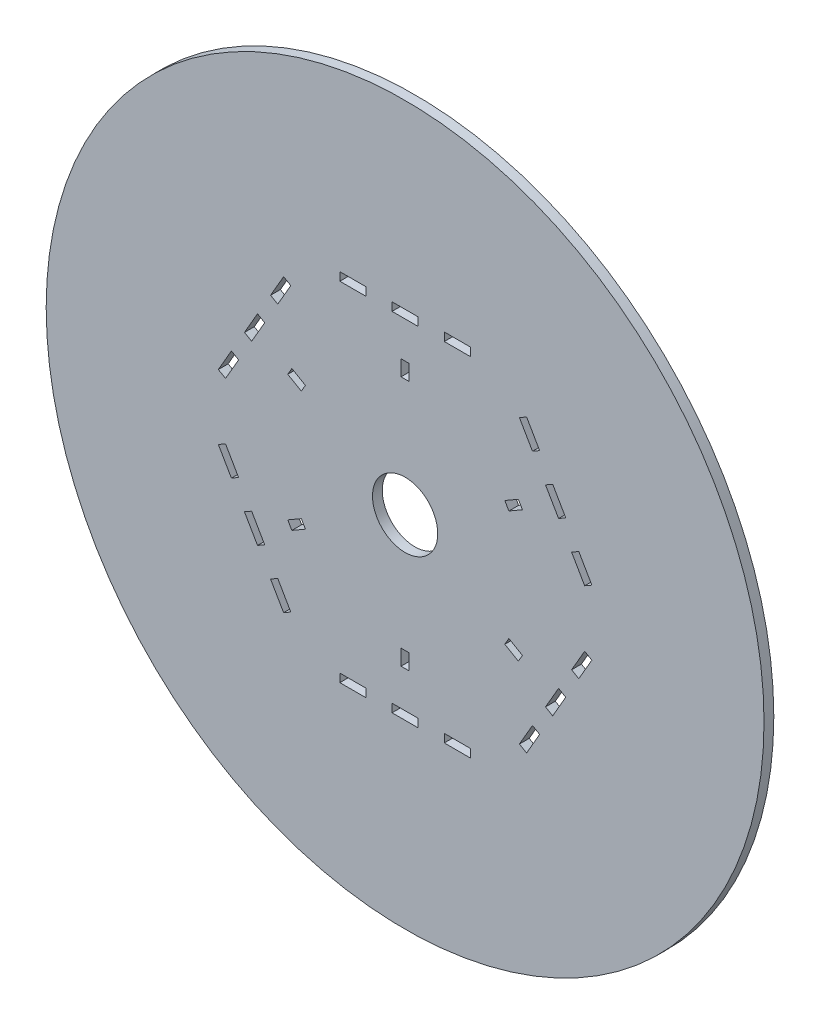
SolidWorks part; units mm, degrees
ref_plane "Front Plane" through (0, 0, 0) normal (0, 0, 1) x (1, 0, 0)
ref_plane "Top Plane" through (0, 0, 0) normal (0, 1, 0) x (1, 0, 0)
ref_plane "Right Plane" through (0, 0, 0) normal (1, 0, 0) x (0, 0, -1)
sketch "Sketch1" plane through (0, 0, 0) normal (0, 0, 1) x (1, 0, 0)
  line L0 (5, 68.175) -> (-5, 68.175)
  line L1 (-5, 68.175) -> (-5, 65)
  line L2 (-5, 65) -> (5, 65)
  line L3 (-15, 68.175) -> (-5, 68.175) construction
  line L4 (-15, 68.175) -> (-25, 68.175)
  line L5 (-15, 68.175) -> (-15, 65)
  line L6 (-15, 65) -> (-25, 65)
  line L7 (-25, 68.175) -> (-25, 65)
  line L8 (25, 68.175) -> (25, 65)
  line L9 (15, 65) -> (25, 65)
  line L10 (15, 68.175) -> (15, 65)
  line L11 (15, 68.175) -> (25, 68.175)
  line L12 (15, 68.175) -> (5, 68.175) construction
  line L13 (5, 68.175) -> (5, 65)
  line L14 (1.5625, 51) -> (-1.5625, 51)
  line L15 (-1.5625, 51) -> (-1.5625, 45)
  line L16 (-1.5625, 45) -> (1.5625, 45)
  line L17 (1.5625, 51) -> (1.5625, 45)
  line L18 (0, 65) -> (0, 51) construction
  line L19 (0, 45) -> (0, 0) construction
  line L20 (61.5413, 29.7574) -> (56.5413, 38.4176)
  line L21 (56.5413, 38.4176) -> (53.7917, 36.8301)
  line L22 (53.7917, 36.8301) -> (58.7917, 28.1699)
  line L23 (51.5413, 47.0779) -> (46.5413, 55.7381)
  line L24 (51.5413, 47.0779) -> (48.7917, 45.4904)
  line L25 (48.7917, 45.4904) -> (43.7917, 54.1506)
  line L26 (46.5413, 55.7381) -> (43.7917, 54.1506)
  line L27 (71.5413, 12.4369) -> (68.7917, 10.8494)
  line L28 (63.7917, 19.5096) -> (68.7917, 10.8494)
  line L29 (66.5413, 21.0971) -> (63.7917, 19.5096)
  line L30 (66.5413, 21.0971) -> (71.5413, 12.4369)
  line L31 (61.5413, 29.7574) -> (58.7917, 28.1699)
  line L32 (44.9485, 24.1468) -> (43.386, 26.8532)
  line L33 (43.386, 26.8532) -> (38.1899, 23.8532)
  line L34 (38.1899, 23.8532) -> (39.7524, 21.1468)
  line L35 (44.9485, 24.1468) -> (39.7524, 21.1468)
  line L36 (51.5413, 47.0779) -> (56.5413, 38.4176) construction
  line L37 (66.5413, 21.0971) -> (61.5413, 29.7574) construction
  line L38 (56.2917, 32.5) -> (44.1673, 25.5) construction
  line L39 (56.5413, -38.4176) -> (61.5413, -29.7574)
  line L40 (61.5413, -29.7574) -> (58.7917, -28.1699)
  line L41 (58.7917, -28.1699) -> (53.7917, -36.8301)
  line L42 (66.5413, -21.0971) -> (71.5413, -12.4369)
  line L43 (66.5413, -21.0971) -> (63.7917, -19.5096)
  line L44 (63.7917, -19.5096) -> (68.7917, -10.8494)
  line L45 (71.5413, -12.4369) -> (68.7917, -10.8494)
  line L46 (46.5413, -55.7381) -> (43.7917, -54.1506)
  line L47 (48.7917, -45.4904) -> (43.7917, -54.1506)
  line L48 (51.5413, -47.0779) -> (48.7917, -45.4904)
  line L49 (51.5413, -47.0779) -> (46.5413, -55.7381)
  line L50 (56.5413, -38.4176) -> (53.7917, -36.8301)
  line L51 (43.386, -26.8532) -> (44.9485, -24.1468)
  line L52 (44.9485, -24.1468) -> (39.7524, -21.1468)
  line L53 (39.7524, -21.1468) -> (38.1899, -23.8532)
  line L54 (43.386, -26.8532) -> (38.1899, -23.8532)
  line L55 (66.5413, -21.0971) -> (61.5413, -29.7574) construction
  line L56 (51.5413, -47.0779) -> (56.5413, -38.4176) construction
  line L57 (56.2917, -32.5) -> (44.1673, -25.5) construction
  line L58 (-5, -68.175) -> (5, -68.175)
  line L59 (5, -68.175) -> (5, -65)
  line L60 (5, -65) -> (-5, -65)
  line L61 (15, -68.175) -> (25, -68.175)
  line L62 (15, -68.175) -> (15, -65)
  line L63 (15, -65) -> (25, -65)
  line L64 (25, -68.175) -> (25, -65)
  line L65 (-25, -68.175) -> (-25, -65)
  line L66 (-15, -65) -> (-25, -65)
  line L67 (-15, -68.175) -> (-15, -65)
  line L68 (-15, -68.175) -> (-25, -68.175)
  line L69 (-5, -68.175) -> (-5, -65)
  line L70 (-1.5625, -51) -> (1.5625, -51)
  line L71 (1.5625, -51) -> (1.5625, -45)
  line L72 (1.5625, -45) -> (-1.5625, -45)
  line L73 (-1.5625, -51) -> (-1.5625, -45)
  line L74 (15, -68.175) -> (5, -68.175) construction
  line L75 (-15, -68.175) -> (-5, -68.175) construction
  line L76 (0, -65) -> (0, -51) construction
  line L77 (-61.5413, -29.7574) -> (-56.5413, -38.4176)
  line L78 (-56.5413, -38.4176) -> (-53.7917, -36.8301)
  line L79 (-53.7917, -36.8301) -> (-58.7917, -28.1699)
  line L80 (-51.5413, -47.0779) -> (-46.5413, -55.7381)
  line L81 (-51.5413, -47.0779) -> (-48.7917, -45.4904)
  line L82 (-48.7917, -45.4904) -> (-43.7917, -54.1506)
  line L83 (-46.5413, -55.7381) -> (-43.7917, -54.1506)
  line L84 (-71.5413, -12.4369) -> (-68.7917, -10.8494)
  line L85 (-63.7917, -19.5096) -> (-68.7917, -10.8494)
  line L86 (-66.5413, -21.0971) -> (-63.7917, -19.5096)
  line L87 (-66.5413, -21.0971) -> (-71.5413, -12.4369)
  line L88 (-61.5413, -29.7574) -> (-58.7917, -28.1699)
  line L89 (-44.9485, -24.1468) -> (-43.386, -26.8532)
  line L90 (-43.386, -26.8532) -> (-38.1899, -23.8532)
  line L91 (-38.1899, -23.8532) -> (-39.7524, -21.1468)
  line L92 (-44.9485, -24.1468) -> (-39.7524, -21.1468)
  line L93 (-51.5413, -47.0779) -> (-56.5413, -38.4176) construction
  line L94 (-66.5413, -21.0971) -> (-61.5413, -29.7574) construction
  line L95 (-56.2917, -32.5) -> (-44.1673, -25.5) construction
  line L96 (-56.5413, 38.4176) -> (-61.5413, 29.7574)
  line L97 (-61.5413, 29.7574) -> (-58.7917, 28.1699)
  line L98 (-58.7917, 28.1699) -> (-53.7917, 36.8301)
  line L99 (-66.5413, 21.0971) -> (-71.5413, 12.4369)
  line L100 (-66.5413, 21.0971) -> (-63.7917, 19.5096)
  line L101 (-63.7917, 19.5096) -> (-68.7917, 10.8494)
  line L102 (-71.5413, 12.4369) -> (-68.7917, 10.8494)
  line L103 (-46.5413, 55.7381) -> (-43.7917, 54.1506)
  line L104 (-48.7917, 45.4904) -> (-43.7917, 54.1506)
  line L105 (-51.5413, 47.0779) -> (-48.7917, 45.4904)
  line L106 (-51.5413, 47.0779) -> (-46.5413, 55.7381)
  line L107 (-56.5413, 38.4176) -> (-53.7917, 36.8301)
  line L108 (-43.386, 26.8532) -> (-44.9485, 24.1468)
  line L109 (-44.9485, 24.1468) -> (-39.7524, 21.1468)
  line L110 (-39.7524, 21.1468) -> (-38.1899, 23.8532)
  line L111 (-43.386, 26.8532) -> (-38.1899, 23.8532)
  line L112 (-66.5413, 21.0971) -> (-61.5413, 29.7574) construction
  line L113 (-51.5413, 47.0779) -> (-56.5413, 38.4176) construction
  line L114 (-56.2917, 32.5) -> (-44.1673, 25.5) construction
  circle A0 centre (0, 0) radius 137.5
  circle A1 centre (0, 0) radius 12.5
  point P3 (0, 68.175)
  point P13 (0, 65)
  point P18 (0, 45)
  point P19 (0, 51)
  point P31 (59.0413, 34.0875)
  point P41 (56.2917, 32.5)
  point P46 (38.9711, 22.5)
  point P47 (44.1673, 25.5)
  point P53 (59.0413, -34.0875)
  point P63 (56.2917, -32.5)
  point P68 (38.9711, -22.5)
  point P69 (44.1673, -25.5)
  point P75 (0, -68.175)
  point P85 (0, -65)
  point P90 (0, -45)
  point P91 (0, -51)
  point P97 (-59.0413, -34.0875)
  point P107 (-56.2917, -32.5)
  point P112 (-38.9711, -22.5)
  point P113 (-44.1673, -25.5)
  point P119 (-59.0413, 34.0875)
  point P129 (-56.2917, 32.5)
  point P134 (-38.9711, 22.5)
  point P135 (-44.1673, 25.5)
  point P138 (0, 0)
  dimension "D8" = 275
  dimension "D9" = 25
  dimension "D1" = 3.175
  dimension "D2" = 10
  dimension "D3" = 1.5625
  dimension "D4" = 6
  dimension "D5" = 14
  dimension "D6" = 45
  dimension "D7" = 6
extrude "Boss-Extrude1" add sketch "Sketch1" along normal mid plane 3.75
